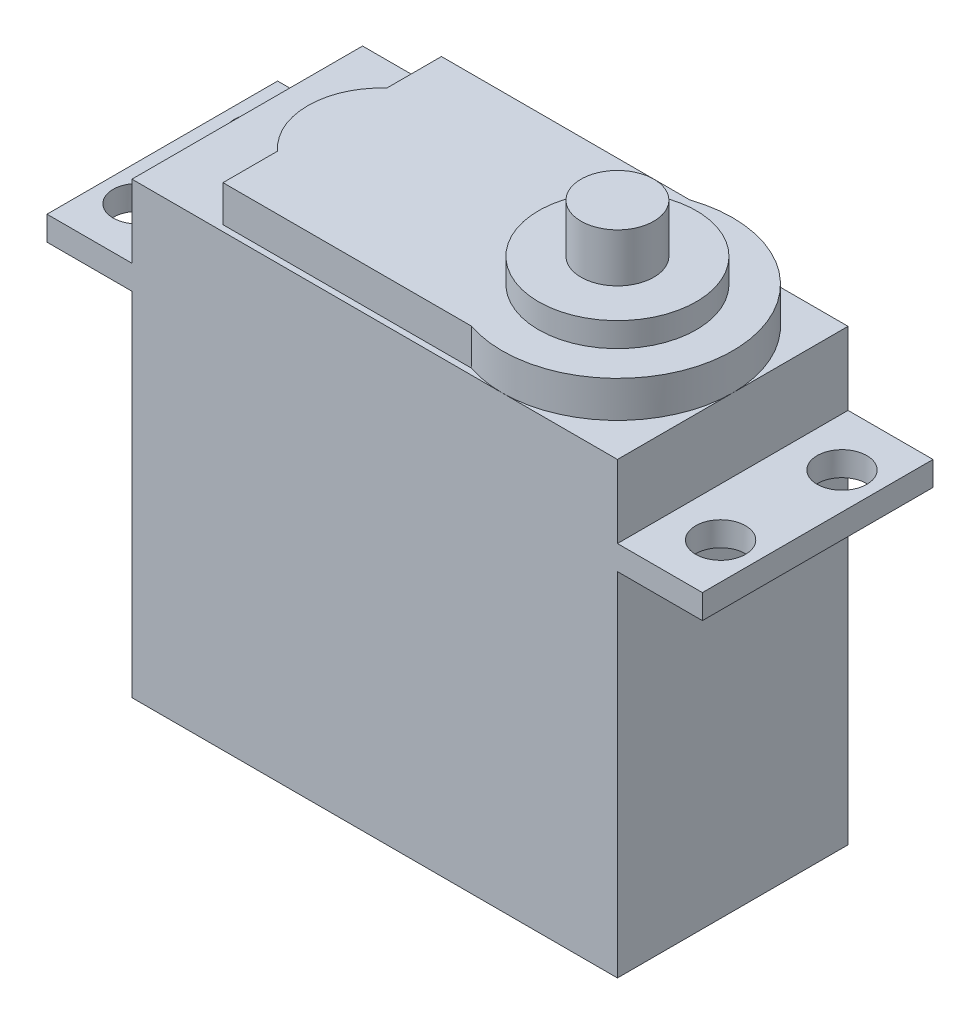
SolidWorks part; units mm, degrees
ref_plane "Front Plane" through (0, 0, 0) normal (0, 0, 1) x (1, 0, 0)
ref_plane "Top Plane" through (0, 0, 0) normal (0, 1, 0) x (1, 0, 0)
ref_plane "Right Plane" through (0, 0, 0) normal (1, 0, 0) x (0, 0, -1)
sketch "Sketch1" plane through (0, 0, 0) normal (0, 0, 1) x (1, 0, 0)
  line L1 (0, 0) -> (40, 0)
  line L2 (0, 0) -> (0, 37)
  line L3 (0, 37) -> (40, 37)
  line L4 (40, 0) -> (40, 37)
  dimension "D1" = 40
  dimension "D2" = 37
extrude "Boss-Extrude1" add sketch "Sketch1" along normal blind 19
sketch "Sketch2" plane through (0, 37, 0) normal (0, 1, 0) x (1, 0, 0)
  line L0 (40, 0) -> (0, 0) construction
  line L1 (40, -19) -> (0, -19) construction
  line L2 (40, -19) -> (40, 0) construction
  line L3 (40, 0) -> (0, 0) construction
  line L4 (40, -19) -> (0, -19) construction
  line L5 (40, -19) -> (40, 0) construction
  line L6 (7, -0.5) -> (7, -5)
  line L7 (7, -18.5) -> (27.4586, -18.5)
  line L8 (7, -0.5) -> (27.4586, -0.5)
  line L9 (7, -14) -> (7, -18.5)
  arc A0 (27.4586, -18.5) -> (27.4586, -0.5) centre (30.5, -9.5) ccw
  arc A1 (7, -5) -> (7, -14) centre (11.0625, -9.5) ccw
  point P8 (21, -9.5)
  point P14 (5, -9.5)
  dimension "D3" = 9
  dimension "D1" = 18
  dimension "D2" = 33
  dimension "D4" = 2
extrude "Boss-Extrude2" add sketch "Sketch2" along normal blind 3
sketch "Sketch3" plane through (0, 40, 0) normal (0, 1, 0) x (1, 0, 0)
  circle A0 centre (30.5, -9.5) radius 6.5
  dimension "D1" = 13
extrude "Boss-Extrude3" add sketch "Sketch3" along normal blind 2
sketch "Sketch5" plane through (0, 42, 0) normal (0, 1, 0) x (1, 0, 0)
  circle A0 centre (30.5, -9.5) radius 3
  dimension "D1" = 6
extrude "Boss-Extrude4" add sketch "Sketch5" along normal blind 4
ref_plane "Plane1" through (0, 29, 0) normal (0, -1, 0) x (-1, 0, 0)
sketch "Sketch6" plane through (0, 29, 0) normal (0, -1, 0) x (-1, 0, 0)
  line L1 (7, -19) -> (-47, -19)
  line L2 (7, -19) -> (7, 0)
  line L3 (7, 0) -> (-47, 0)
  line L4 (0, 0) -> (-40, 0)
  line L5 (-40, 0) -> (-40, -19)
  line L6 (-40, -19) -> (0, -19)
  line L7 (0, -19) -> (0, 0)
  line L8 (0, 0) -> (-40, 0) construction
  line L9 (-40, 0) -> (-40, -19) construction
  line L10 (-40, -19) -> (0, -19) construction
  line L11 (0, -19) -> (0, 0) construction
  line L12 (-47, -19) -> (-47, 0)
  point P8 (-20, -19)
  point P9 (-20, -19)
  point P10 (-20, 0)
  point P11 (-20, 0)
  dimension "D2" = 54
  dimension "D1" = 0
extrude "Boss-Extrude5" add sketch "Sketch6" against normal blind 2
sketch "Sketch7" plane through (0, 31, 0) normal (0, 1, 0) x (1, 0, 0)
  line L0 (-7, -19) -> (-7, 0) construction
  line L1 (47, 0) -> (47, -19) construction
  line L2 (-7, -19) -> (-7, 0) construction
  line L3 (47, 0) -> (47, -19) construction
  line L4 (-4, -4.5) -> (-4, -14.5) construction
  line L5 (44, -4.5) -> (44, -14.5) construction
  circle A0 centre (-4, -4.5) radius 2.05
  circle A1 centre (-4, -14.5) radius 2.05
  circle A2 centre (44, -4.5) radius 2.05
  circle A3 centre (44, -14.5) radius 2.05
  point P8 (44, -9.5)
  point P9 (47, -9.5)
  point P11 (-4, -9.5)
  point P12 (-7, -9.5)
  dimension "D4" = 4.1
  dimension "D1" = 10
  dimension "D2" = 3
  dimension "D3" = 3
extrude "Cut-Extrude1" cut sketch "Sketch7" against normal up to surface (2 mm away) up to face at (-3.5, 29, 9.5)
